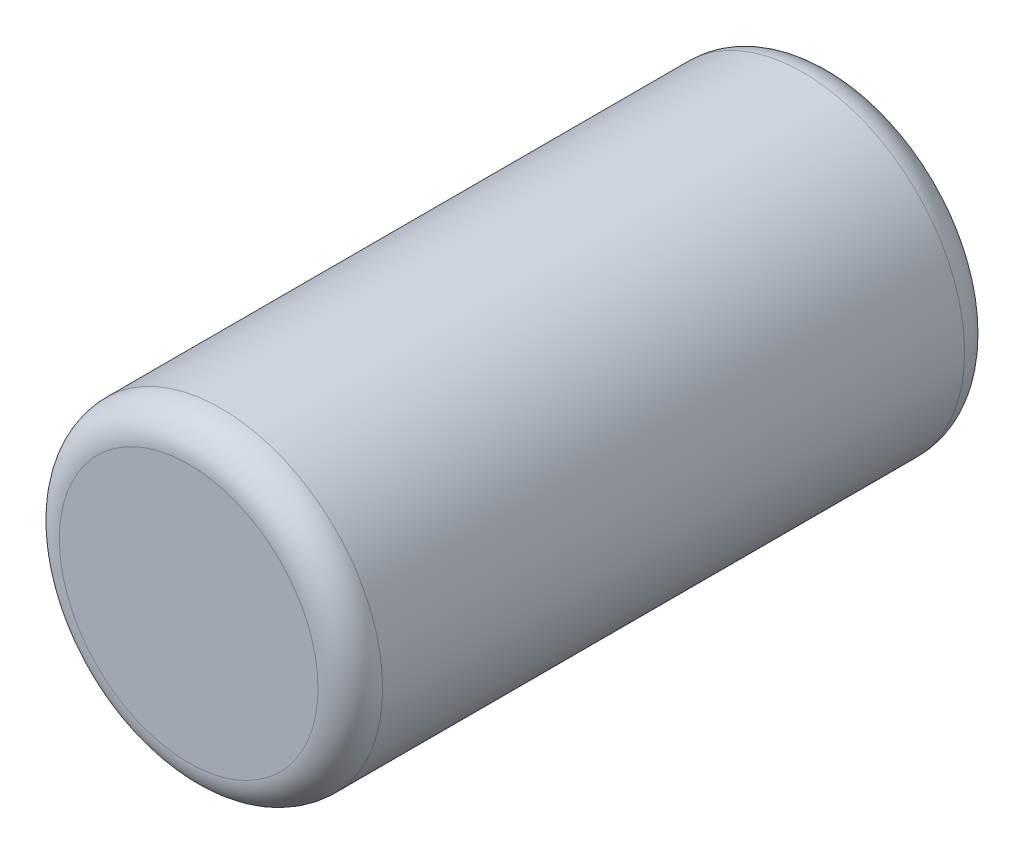
SolidWorks part; units mm, degrees
ref_plane "Front Plane" through (0, 0, 0) normal (0, 0, 1) x (1, 0, 0)
ref_plane "Top Plane" through (0, 0, 0) normal (0, 1, 0) x (1, 0, 0)
ref_plane "Right Plane" through (0, 0, 0) normal (1, 0, 0) x (0, 0, -1)
sketch "Sketch1" plane through (0, 0, 0) normal (0, 0, 1) x (1, 0, 0)
  circle A0 centre (0, 0) radius 1.27
  dimension "D1" = 2.54
extrude "Boss-Extrude1" add sketch "Sketch1" along normal mid plane 5.08
fillet "Fillet2" radius 0.254 2 edges at (1.27, 0, -2.54) (1.27, 0, 2.54)
